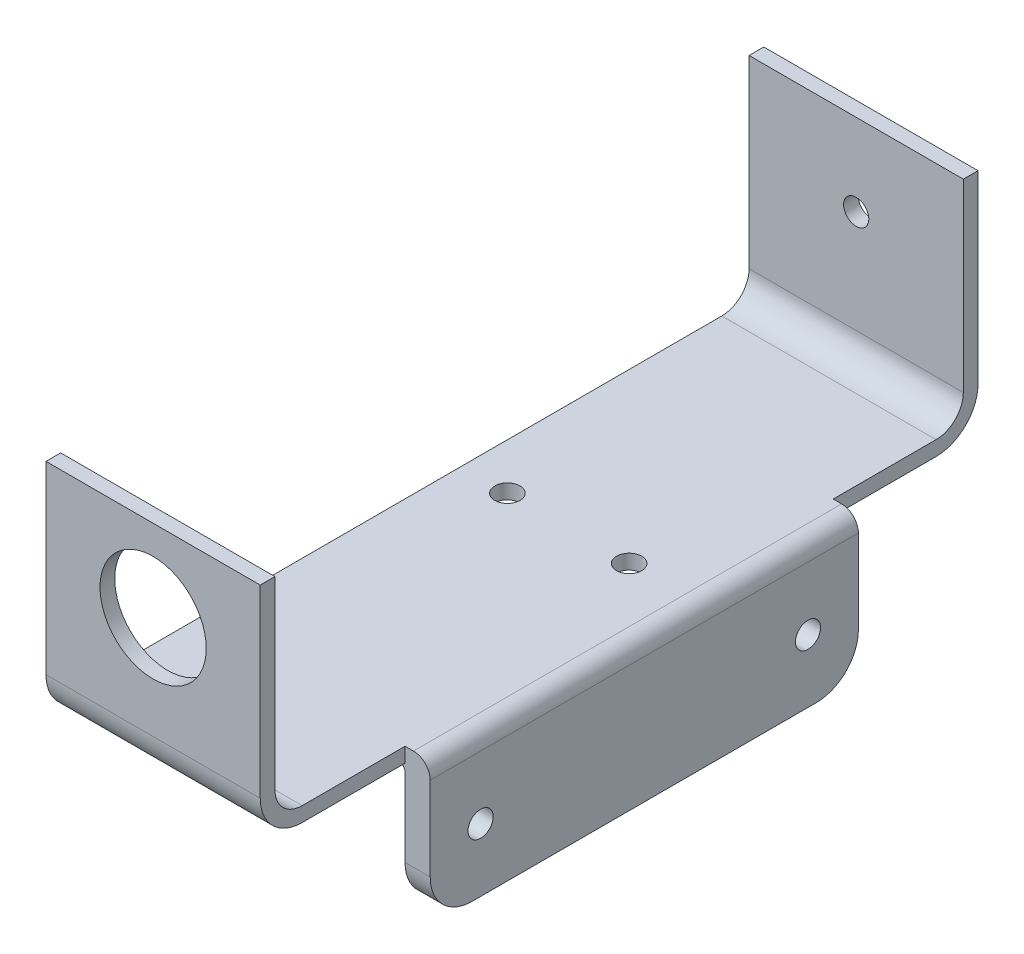
SolidWorks part; units mm, degrees
material "1023 Tôle d'acier au carbone (SS)"
ref_plane "Plan de face" through (0, 0, 0) normal (0, 0, 1) x (1, 0, 0)
ref_plane "Plan de dessus" through (0, 0, 0) normal (0, 1, 0) x (1, 0, 0)
ref_plane "Plan de droite" through (0, 0, 0) normal (1, 0, 0) x (0, 0, -1)
sketch "Esquisse1" plane through (0, 0, 0) normal (1, 0, 0) x (0, 0, -1)
  line L0 (0, 27) -> (0, 5)
  line L1 (5, 0) -> (80.5, 0)
  line L2 (85.5, 5) -> (85.5, 27)
  line L3 (1.75, 27) -> (1.75, 5)
  line L4 (5, 1.75) -> (80.5, 1.75)
  line L5 (83.75, 5) -> (83.75, 27)
  line L6 (0, 27) -> (1.75, 27)
  line L7 (83.75, 27) -> (85.5, 27)
  arc A0 (80.5, 0) -> (85.5, 5) centre (80.5, 5) ccw
  arc A1 (0, 5) -> (5, 0) centre (5, 5) ccw
  arc A2 (1.75, 5) -> (5, 1.75) centre (5, 5) ccw
  arc A3 (80.5, 1.75) -> (83.75, 5) centre (80.5, 5) ccw
  point P7 (85.5, 0)
  point P10 (0, 0)
  dimension "D3" = 5
  dimension "D1" = 85.5
  dimension "D2" = 27
  dimension "D4" = 1.75
extrude "Boss.-Extru.1" add sketch "Esquisse1" along normal blind 25.52
sketch "Esquisse2" plane through (0, 0, 0) normal (0, 0, 1) x (1, 0, 0)
  line L0 (25.52, 27) -> (0, 27) construction
  circle A0 centre (12.76, 17.25) radius 6.325
  dimension "D1" = 12.65
  dimension "D2" = 9.75
extrude "Enlèv. mat.-Extru.1" cut sketch "Esquisse2" against normal up to surface (1.75 mm away) up to face at (12.76, 16, -1.75)
sketch "Esquisse3" plane through (0, 0, -85.5) normal (0, 0, -1) x (-1, 0, 0)
  line L0 (-25.52, 27) -> (0, 27) construction
  circle A0 centre (-12.76, 17.25) radius 1.5
  dimension "D1" = 3
  dimension "D2" = 9.75
extrude "Enlèv. mat.-Extru.2" cut sketch "Esquisse3" against normal blind 25.52
sketch "Esquisse6" plane through (0, 1.75, 0) normal (0, 1, 0) x (1, 0, 0)
  line L0 (25.52, 80.5) -> (25.52, 5) construction
  line L1 (25.52, 68.25) -> (28.52, 68.25)
  line L2 (25.52, 68.25) -> (25.52, 17.25)
  line L3 (25.52, 17.25) -> (28.52, 17.25)
  line L4 (28.52, 68.25) -> (28.52, 17.25)
  line L5 (28.52, 42.75) -> (25.52, 42.75) construction
  line L6 (0, 42.75) -> (25.52, 42.75) construction
  line L7 (0, 80.5) -> (0, 5) construction
  dimension "D1" = 51
  dimension "D2" = 3
extrude "Boss.-Extru.2" add sketch "Esquisse6" against normal blind 17
fillet "Congé1" radius 2 1 edges at (28.52, 1.75, -42.75)
fillet "Congé2" radius 1 1 edges at (25.52, 0, -42.75)
sketch "Esquisse7" plane through (28.52, 0, 0) normal (1, 0, 0) x (0, 0, -1)
  line L0 (17.25, -7.75) -> (68.25, -7.75) construction
  line L1 (17.25, -15.25) -> (17.25, -0.25) construction
  line L2 (68.25, -15.25) -> (68.25, -0.25) construction
  line L3 (23.25, -7.75) -> (62.25, -7.75) construction
  line L4 (42.75, -15.25) -> (42.75, -0.25) construction
  line L5 (17.25, -15.25) -> (68.25, -15.25) construction
  line L6 (68.25, -0.25) -> (17.25, -0.25) construction
  line L7 (42.75, -7.75) -> (42.75, -4.7152) construction
  circle A0 centre (23.25, -7.75) radius 1.5
  circle A1 centre (62.25, -7.75) radius 1.5
  dimension "D2" = 3
  dimension "D1" = 39
extrude "Enlèv. mat.-Extru.3" cut sketch "Esquisse7" against normal through all
fillet "Congé3" radius 5 2 edges at (27.02, -15.25, -68.25) (27.02, -15.25, -17.25)
sketch "Esquisse8" plane through (0, 1.75, 0) normal (0, 1, 0) x (1, 0, 0)
  line L0 (12.76, 80.5) -> (12.76, 0) construction
  line L1 (25.52, 80.5) -> (0, 80.5) construction
  circle A0 centre (20.01, 49.45) radius 1.5
  circle A1 centre (5.51, 49.45) radius 1.5
  dimension "D2" = 3
  dimension "D1" = 49.45
  dimension "D3" = 14.5
  dimension "D4" = 7.25
extrude "Enlèv. mat.-Extru.4" cut sketch "Esquisse8" against normal through all
